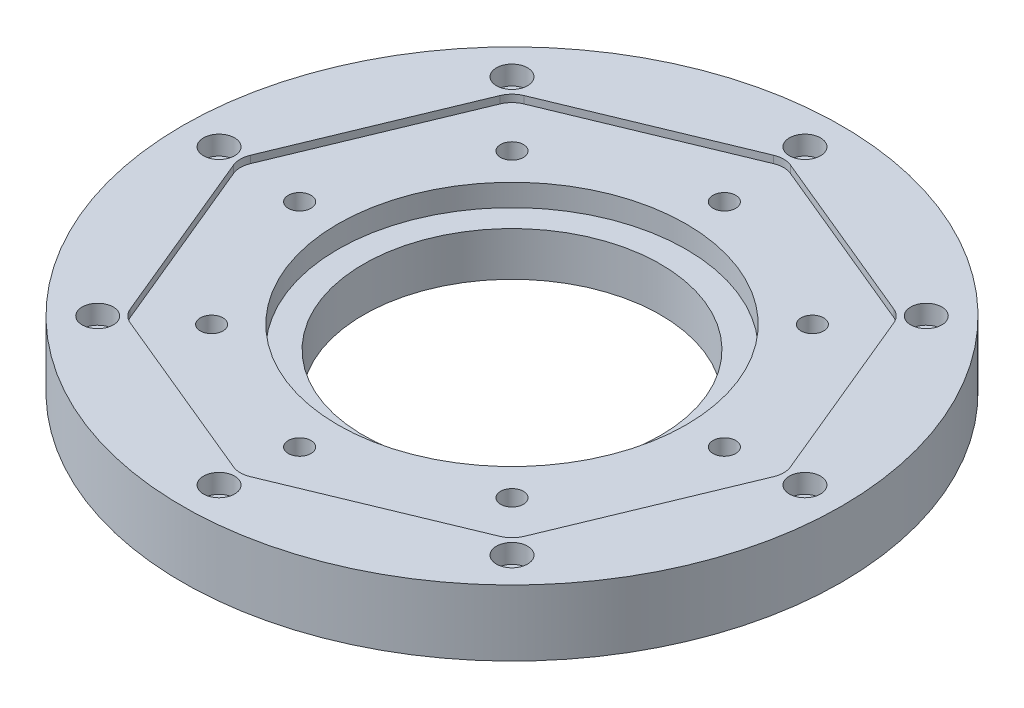
SolidWorks part; units mm, degrees
material "PVC rigide"
ref_plane "Plan de face" through (0, 0, 0) normal (0, 0, 1) x (1, 0, 0)
ref_plane "Plan de dessus" through (0, 0, 0) normal (0, 1, 0) x (1, 0, 0)
ref_plane "Plan de droite" through (0, 0, 0) normal (1, 0, 0) x (0, 0, -1)
sketch "Esquisse1" plane through (0, 0, 0) normal (0, 0, 1) x (1, 0, 0)
  line L0 (0, 0) -> (0, 73.3911) construction
  line L1 (-40.55, 0) -> (-40.55, 12)
  line L2 (-40.55, 12) -> (-47.55, 12)
  line L3 (-47.55, 12) -> (-47.55, 20)
  line L4 (-47.55, 20) -> (-65, 20)
  line L5 (-65, 2) -> (-65, 0)
  line L6 (-65, 0) -> (-50.3, 0)
  line L7 (-50.3, 0) -> (-50.3, 6)
  line L8 (-50.3, 6) -> (-47.1, 6)
  line L9 (-47.1, 6) -> (-47.1, 0)
  line L10 (-47.1, 0) -> (-40.55, 0)
  line L11 (-58, 20) -> (-58, 0) construction
  line L12 (-65, 2) -> (-90, 2)
  line L13 (-90, 2) -> (-90, 20)
  line L14 (-90, 20) -> (-65, 20)
  dimension "D1" = 7
  dimension "D2" = 95.1
  dimension "D3" = 6
  dimension "D4" = 20
  dimension "D5" = 6
  dimension "D6" = 58
  dimension "D7" = 94.2
  dimension "D8" = 100.6
  dimension "D9" = 130
  dimension "D10" = 90
  dimension "D11" = 2
revolve "Révolution1" add sketch "Esquisse1" angle 360 about L0
sketch "Esquisse2" plane through (0, 0, 0) normal (0, -1, 0) x (1, 0, 0)
  line L0 (0, 0) -> (0, 65) construction
  circle A0 centre (0, 0) radius 65 construction
  circle A1 centre (0, 58) radius 3.1
  circle A2 centre (41.0122, 41.0122) radius 3.1
  circle A3 centre (58, 0) radius 3.1
  circle A4 centre (41.0122, -41.0122) radius 3.1
  circle A5 centre (0, -58) radius 3.1
  circle A6 centre (-41.0122, -41.0122) radius 3.1
  circle A7 centre (-58, 0) radius 3.1
  circle A8 centre (-41.0122, 41.0122) radius 3.1
  dimension "D3" = 6.2
  dimension "D1" = 58
  dimension "D2" = 8
extrude "Enlèv. mat.-Extru.1" cut sketch "Esquisse2" against normal through all
sketch "Esquisse3" plane through (0, 20, 0) normal (0, 1, 0) x (1, 0, 0)
  line L0 (-52.8103, 52.8103) -> (-74.6851, 0)
  line L1 (-52.8103, -52.8103) -> (0, -74.6851)
  line L2 (0, -74.6851) -> (52.8103, -52.8103)
  line L3 (52.8103, -52.8103) -> (74.6851, 0)
  line L4 (74.6851, 0) -> (52.8103, 52.8103)
  line L5 (52.8103, 52.8103) -> (0, 74.6851)
  line L6 (0, 74.6851) -> (-52.8103, 52.8103)
  line L7 (-74.6851, 0) -> (-52.8103, -52.8103)
  line L8 (0, 0) -> (-58, 0) construction
  circle A1 centre (0, 0) radius 69 construction
  dimension "D1" = 138
extrude "Enlèv. mat.-Extru.2" cut sketch "Esquisse3" against normal blind 2
sketch "Esquisse4" plane through (0, 20, 0) normal (0, 1, 0) x (1, 0, 0)
  circle A0 centre (0, 0) radius 80 construction
  circle A1 centre (0, 80) radius 2.6
  circle A2 centre (56.5685, 56.5685) radius 2.6
  circle A3 centre (80, 0) radius 2.6
  circle A4 centre (56.5685, -56.5685) radius 2.6
  circle A5 centre (0, -80) radius 2.6
  circle A6 centre (-56.5685, -56.5685) radius 2.6
  circle A7 centre (-80, 0) radius 2.6
  circle A8 centre (-56.5685, 56.5685) radius 2.6
  dimension "D1" = 160
  dimension "D2" = 5.2
  dimension "D3" = 8
extrude "Enlèv. mat.-Extru.3" cut sketch "Esquisse4" against normal through all
sketch "Esquisse5" plane through (0, 20, 0) normal (0, 1, 0) x (1, 0, 0)
  circle A0 centre (0, 80) radius 4.25
  circle A1 centre (56.5685, 56.5685) radius 4.25
  circle A2 centre (80, 0) radius 4.25
  circle A3 centre (56.5685, -56.5685) radius 4.25
  circle A4 centre (0, -80) radius 4.25
  circle A5 centre (-56.5685, -56.5685) radius 4.25
  circle A6 centre (-80, 0) radius 4.25
  circle A7 centre (-56.5685, 56.5685) radius 4.25
  dimension "D1" = 8.5
  dimension "D2" = 8
extrude "Enlèv. mat.-Extru.4" cut sketch "Esquisse5" against normal blind 5.2
fillet "Congé1" radius 6 8 edges at (0, 19, -74.6851) (52.8103, 19, -52.8103) (74.6851, 19, 0) (52.8103, 19, 52.8103) (0, 19, 74.6851) (-52.8103, 19, 52.8103) (-74.6851, 19, 0) (-52.8103, 19, -52.8103)
